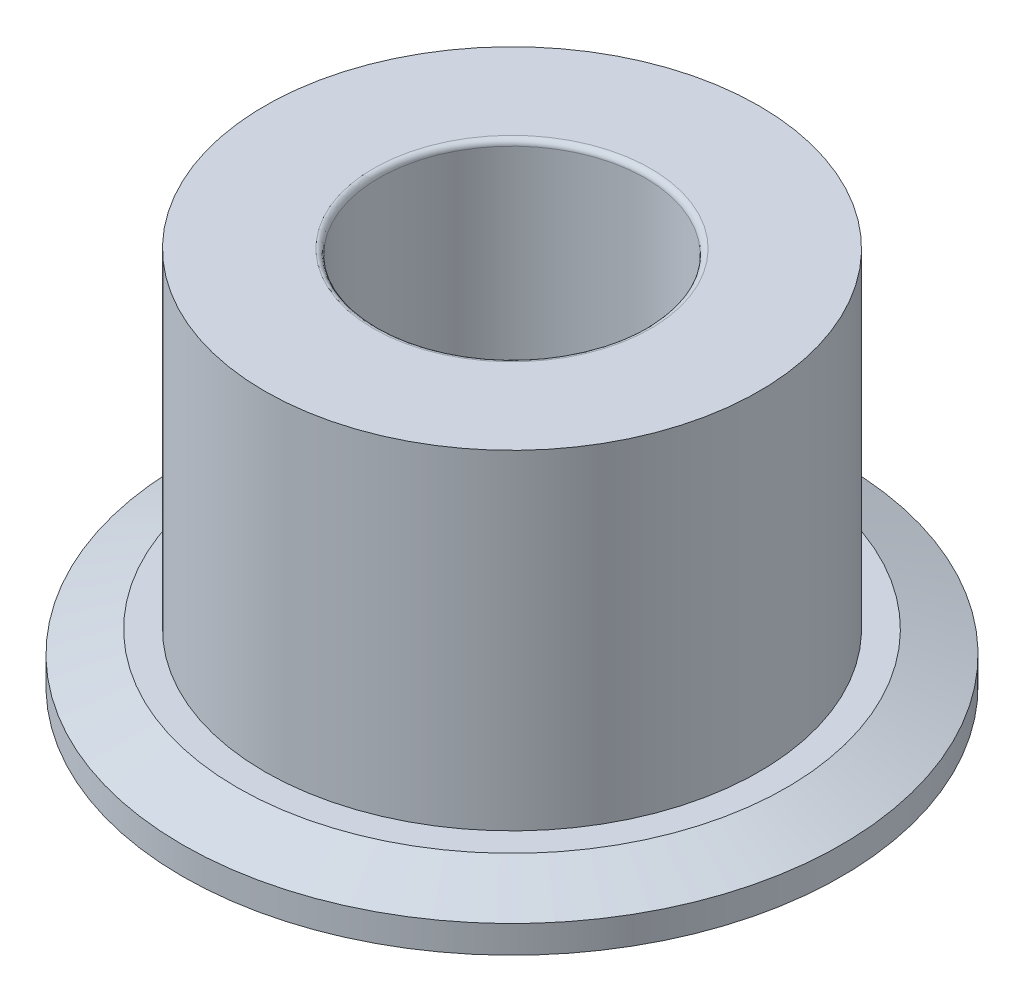
SolidWorks part; units mm, degrees
ref_plane "前视基准面" through (0, 0, 0) normal (0, 0, 1) x (1, 0, 0)
ref_plane "上视基准面" through (0, 0, 0) normal (0, 1, 0) x (1, 0, 0)
ref_plane "右视基准面" through (0, 0, 0) normal (1, 0, 0) x (0, 0, -1)
sketch "草图1" plane through (0, 0, 0) normal (0, 1, 0) x (1, 0, 0)
  line L0 (0, 24.0455) -> (0, -27.7329) construction
  line L1 (-44.7107, 0) -> (48.7055, 0) construction
  circle A0 centre (0, 0) radius 2.425
  circle A1 centre (0, 0) radius 6
  dimension "D1" = 4.85
  dimension "D2" = 12
extrude "凸台-拉伸1" add sketch "草图1" along normal blind 0.9
sketch "草图2" plane through (0, 0.9, 0) normal (0, 1, 0) x (1, 0, 0)
  circle A0 centre (0, 0) radius 4.5
  circle A1 centre (0, 0) radius 2.425
  dimension "D1" = 4.85
  dimension "D2" = 9
extrude "凸台-拉伸2" add sketch "草图2" along normal blind 6
fillet "圆角1" radius 0.1 1 edges at (0, 6.9, 2.425)
chamfer "倒角1" distance 0.4 distance2 1 1 edges at (0, 0.9, 6)
